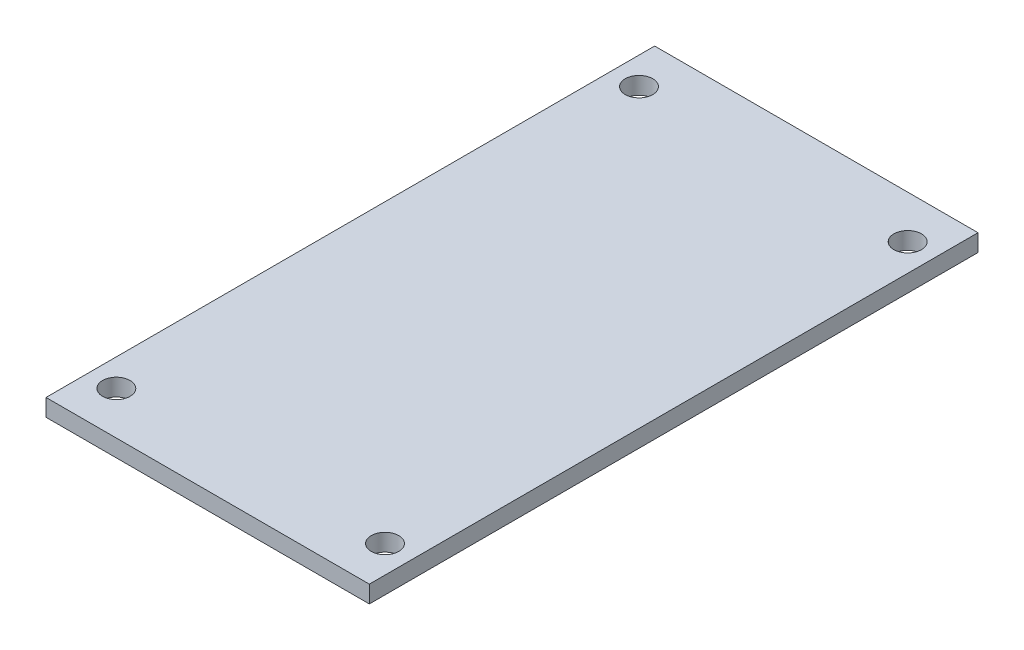
SolidWorks part; units mm, degrees
material "Custom Plastic"
ref_plane "Front Plane" through (0, 0, 0) normal (0, 0, 1) x (1, 0, 0)
ref_plane "Top Plane" through (0, 0, 0) normal (0, 1, 0) x (1, 0, 0)
ref_plane "Right Plane" through (0, 0, 0) normal (1, 0, 0) x (0, 0, -1)
sketch "Sketch1" plane through (0, 0, 0) normal (0, 1, 0) x (1, 0, 0)
  line L0 (-46.441, 0) -> (54.5281, 0) construction
  line L1 (-18.8, -35.39) -> (18.8, -35.39)
  line L2 (-18.8, -35.39) -> (-18.8, 35.39)
  line L3 (-18.8, 35.39) -> (18.8, 35.39)
  line L4 (18.8, -35.39) -> (18.8, 35.39)
  line L5 (-18.8, -35.39) -> (18.8, 35.39) construction
  line L6 (-18.8, 35.39) -> (18.8, -35.39) construction
  line L7 (0, 43.5273) -> (0, -49.7115) construction
  circle A0 centre (15.62, 30.39) radius 1.6
  circle A1 centre (15.62, -30.39) radius 1.6
  circle A2 centre (-15.62, -30.39) radius 1.6
  circle A3 centre (-15.62, 30.39) radius 1.6
  point P0 (0, 0)
  dimension "D1" = 3.2
  dimension "D2" = 37.6
  dimension "D3" = 30.39
  dimension "D4" = 5
  dimension "D5" = 3.18
extrude "Boss-Extrude1" add sketch "Sketch1" along normal blind 2
